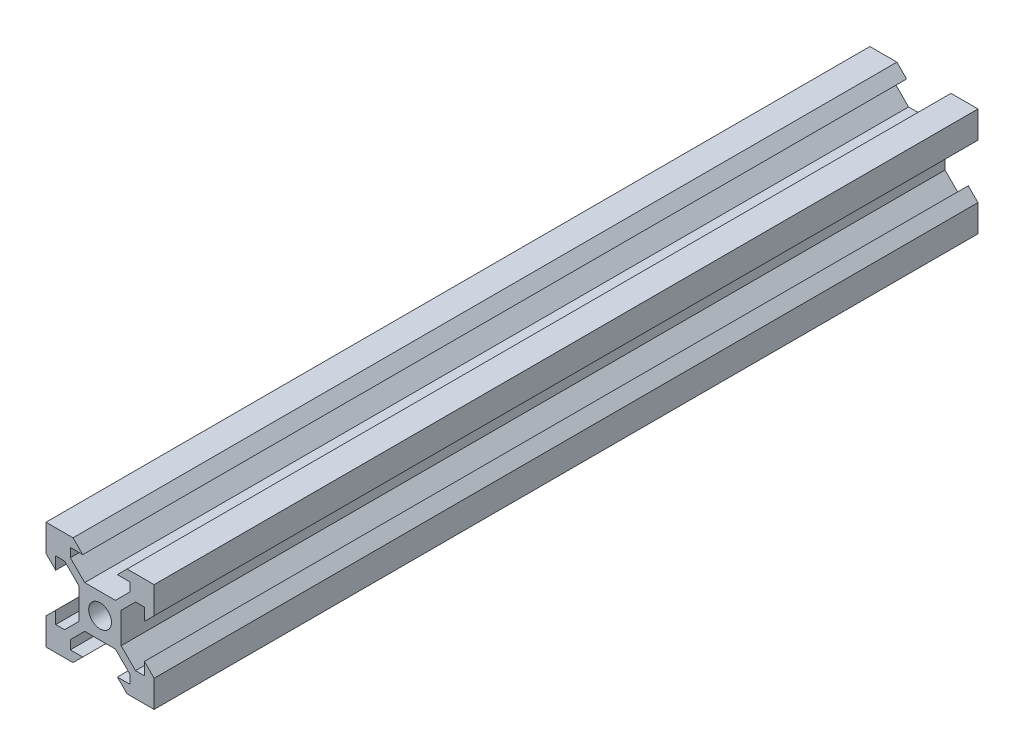
SolidWorks part; units mm, degrees
material "6063-T5"
ref_plane "Front Plane" through (0, 0, 0) normal (0, 0, 1) x (1, 0, 0)
ref_plane "Top Plane" through (0, 0, 0) normal (0, 1, 0) x (1, 0, 0)
ref_plane "Right Plane" through (0, 0, 0) normal (1, 0, 0) x (0, 0, -1)
sketch "Sketch1" plane through (0, 0, 0) normal (0, 0, 1) x (1, 0, 0)
  line L0 (-10, 10) -> (-5, 10)
  line L1 (10, -10) -> (-10, -10) construction
  line L2 (10, -10) -> (10, 10) construction
  line L3 (10, 10) -> (-10, 10) construction
  line L4 (-10, -10) -> (-10, 10) construction
  line L5 (10, -10) -> (-10, 10) construction
  line L6 (10, 10) -> (-10, -10) construction
  line L7 (-5, 10) -> (-3.2, 8.2)
  line L8 (-3.2, 8.2) -> (-5.4993, 8.2)
  line L9 (-5.4993, 8.2) -> (-5.4993, 6.56)
  line L10 (-2.84, 3.9007) -> (2.84, 3.9007)
  line L11 (0, 3.9007) -> (0, 2.1) construction
  line L12 (-5.4993, 6.56) -> (-2.84, 3.9007)
  line L13 (0, 0) -> (0, -13.2939) construction
  line L14 (0, 0) -> (-17.0802, 0) construction
  line L15 (-10, 10) -> (-10, 5)
  line L16 (-10, 5) -> (-8.2, 3.2)
  line L17 (-8.2, 3.2) -> (-8.2, 5.4993)
  line L18 (-8.2, 5.4993) -> (-6.56, 5.4993)
  line L19 (-6.56, 5.4993) -> (-3.9007, 2.84)
  line L20 (-3.9007, 2.84) -> (-3.9007, -2.84)
  line L21 (-3.2, -8.2) -> (-5.4993, -8.2)
  line L22 (-5.4993, -8.2) -> (-5.4993, -6.56)
  line L23 (-5, -10) -> (-3.2, -8.2)
  line L24 (-10, -10) -> (-5, -10)
  line L25 (-10, -10) -> (-10, -5)
  line L26 (-10, -5) -> (-8.2, -3.2)
  line L27 (-8.2, -3.2) -> (-8.2, -5.4993)
  line L28 (-8.2, -5.4993) -> (-6.56, -5.4993)
  line L29 (-6.56, -5.4993) -> (-3.9007, -2.84)
  line L30 (-5.4993, -6.56) -> (-2.84, -3.9007)
  line L31 (-2.84, -3.9007) -> (2.84, -3.9007)
  line L32 (5.4993, 6.56) -> (2.84, 3.9007)
  line L33 (3.2, 8.2) -> (5.4993, 8.2)
  line L34 (5.4993, 8.2) -> (5.4993, 6.56)
  line L35 (5, 10) -> (3.2, 8.2)
  line L36 (10, 10) -> (5, 10)
  line L37 (10, 10) -> (10, 5)
  line L38 (10, 5) -> (8.2, 3.2)
  line L39 (8.2, 3.2) -> (8.2, 5.4993)
  line L40 (8.2, 5.4993) -> (6.56, 5.4993)
  line L41 (6.56, 5.4993) -> (3.9007, 2.84)
  line L42 (3.9007, 2.84) -> (3.9007, -2.84)
  line L43 (6.56, -5.4993) -> (3.9007, -2.84)
  line L44 (8.2, -5.4993) -> (6.56, -5.4993)
  line L45 (8.2, -3.2) -> (8.2, -5.4993)
  line L46 (10, -5) -> (8.2, -3.2)
  line L47 (10, -10) -> (10, -5)
  line L48 (10, -10) -> (5, -10)
  line L49 (5, -10) -> (3.2, -8.2)
  line L50 (3.2, -8.2) -> (5.4993, -8.2)
  line L51 (5.4993, -8.2) -> (5.4993, -6.56)
  line L52 (5.4993, -6.56) -> (2.84, -3.9007)
  circle A0 centre (0, 0) radius 2.1
  arc A1 (0, -2.1) -> (0, 2.1) centre (0, 0) cw construction
  point P0 (0, 0)
  point P25 (-3.9007, 0)
  point P35 (0, 0)
  point P56 (0, -3.9007)
  dimension "D2" = 4.2
  dimension "D1" = 20
  dimension "D3" = 1.64
  dimension "D4" = 1.8
  dimension "D5" = 45
  dimension "D6" = 1.5
  dimension "D7" = 5.68
  dimension "D8" = 5
extrude "Boss-Extrude1" add sketch "Sketch1" along normal mid plane 152.4
